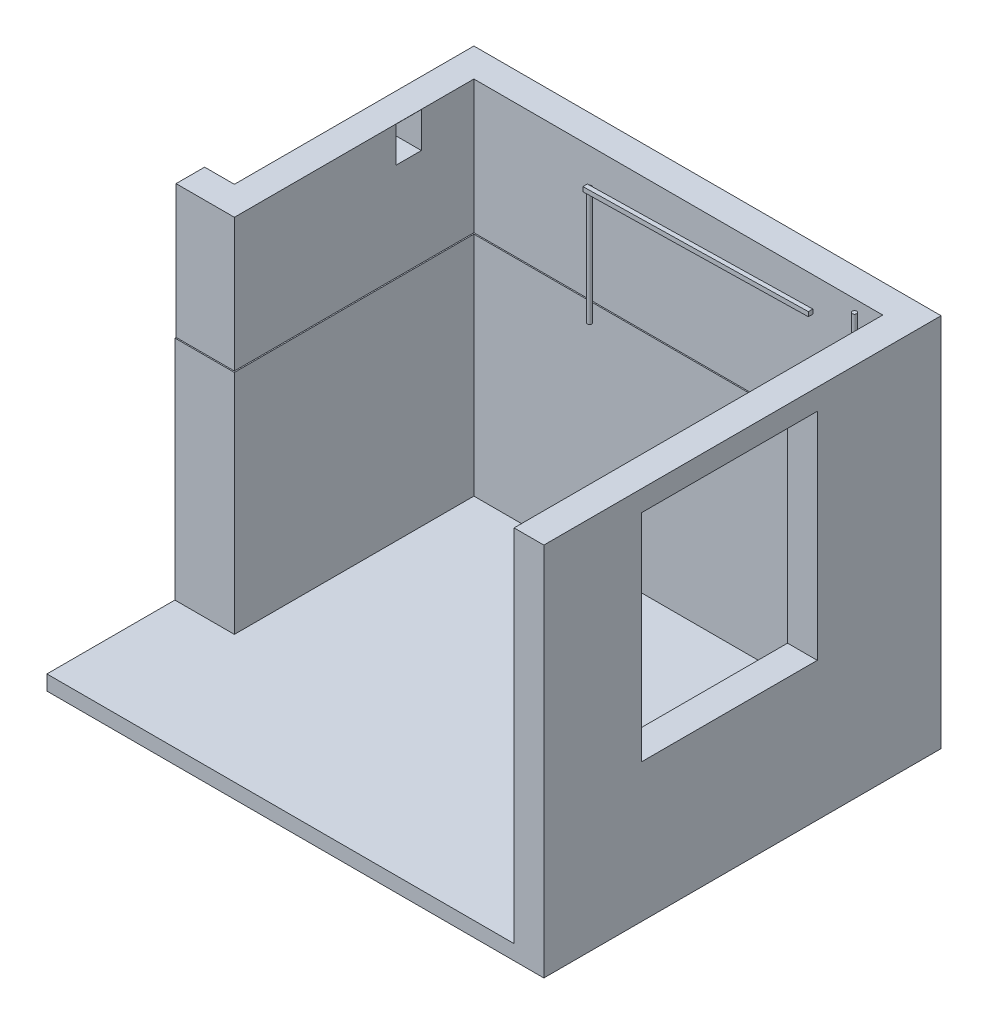
SolidWorks part; units mm, degrees
ref_plane "Спереди" through (0, 0, 0) normal (0, 0, 1) x (1, 0, 0)
ref_plane "Сверху" through (0, 0, 0) normal (0, 1, 0) x (1, 0, 0)
ref_plane "Справа" through (0, 0, 0) normal (1, 0, 0) x (0, 0, -1)
sketch "Эскиз1" plane through (0, 0, 0) normal (0, 1, 0) x (1, 0, 0)
  line L0 (0, 0) -> (0, 1610)
  line L1 (0, 1610) -> (2740, 1610)
  line L2 (2740, 1610) -> (2740, -860)
  line L3 (2740, -860) -> (-400, -860)
  line L5 (-400, 0) -> (0, 0)
  line L6 (2940, 1810) -> (-200, 1810)
  line L7 (-200, 1810) -> (-200, 200)
  line L8 (-200, 200) -> (-400, 200)
  line L9 (-400, 200) -> (-400, 0)
  line L10 (-400, -860) -> (-400, -1060)
  line L11 (-400, -1060) -> (2940, -1060)
  line L12 (2940, -1060) -> (2940, 1810)
  line L13 (2740, 1610) -> (2940, 1610) construction
  line L14 (2740, 1610) -> (2740, 1810) construction
  line L15 (0, 1610) -> (-200, 1610) construction
  line L16 (-200, 200) -> (-200, 0) construction
  line L17 (2740, -860) -> (2740, -1060) construction
  dimension "D1" = 200
  dimension "D2" = 1610
  dimension "D3" = 400
  dimension "D4" = 2470
  dimension "D5" = 2740
extrude "Бобышка-Вытянуть1" add sketch "Эскиз1" along normal blind 2420
sketch "Эскиз2" plane through (0, 0, 0) normal (0, -1, 0) x (1, 0, 0)
  line L0 (-400, 1060) -> (2940, 1060) construction
  line L1 (-400, 1060) -> (2940, 1060)
  line L2 (-200, -200) -> (-400, -200) construction
  line L3 (-200, -200) -> (-400, -200)
  line L4 (-400, -200) -> (-400, 0) construction
  line L5 (-400, -200) -> (-400, 1060)
  line L6 (-200, -1810) -> (-200, -200) construction
  line L7 (2940, -1810) -> (-200, -1810) construction
  line L8 (2940, 1060) -> (2940, -1810) construction
  line L9 (-200, -1810) -> (-200, -200)
  line L10 (2940, -1810) -> (-200, -1810)
  line L11 (2940, 1060) -> (2940, -1810)
extrude "Бобышка-Вытянуть2" add sketch "Эскиз2" along normal blind 100
sketch "Эскиз3" plane through (0, 0, 1060) normal (0, 0, 1) x (1, 0, 0)
  line L12 (-400, 2420) -> (-400, -100)
  line L13 (-400, -100) -> (2940, -100)
  line L14 (2940, -100) -> (2940, 2420)
  line L15 (2940, 2420) -> (-400, 2420)
  line L16 (-400, 2420) -> (-400, -100)
  line L17 (-400, -100) -> (2940, -100)
  line L18 (2940, -100) -> (2940, 2420)
  line L19 (2940, 2420) -> (-400, 2420)
  dimension "D1" = 0
extrude "Вырез-Вытянуть1" cut sketch "Эскиз3" against normal up to surface (200 mm away) up to face at (1170, 1210, 860)
sketch "Эскиз4" plane through (0, 0, 0) normal (1, 0, 0) x (0, 0, -1)
  line L0 (1610, 2420) -> (1610, 0) construction
  line L1 (1095, 2419) -> (1265, 2419)
  line L2 (1095, 2419) -> (1095, 2180)
  line L3 (1095, 2180) -> (1265, 2180)
  line L4 (1265, 2419) -> (1265, 2180)
  line L5 (1095, 2419) -> (1265, 2180) construction
  line L6 (1095, 2180) -> (1265, 2419) construction
  line L7 (0, 0) -> (1610, 0) construction
  point P0 (1180, 2299.5)
  dimension "D1" = 170
  dimension "D2" = 239
  dimension "D3" = 345
  dimension "D4" = 2180
extrude "Вырез-Вытянуть2" cut sketch "Эскиз4" against normal up to surface (200 mm away) up to face at (-200, 1160, -1005)
ref_plane "Плоскость1" through (0, 2235, 0) normal (0, 1, 0) x (1, 0, 0)
sketch "Эскиз5" plane through (0, 2420, 0) normal (0, 1, 0) x (1, 0, 0)
  line L0 (-400, 8) -> (-8, 8)
  line L1 (-400, 200) -> (-400, 0) construction
  line L2 (-8, 8) -> (-8, 1618)
  line L3 (-8, 1618) -> (2740, 1618)
  line L4 (2740, 1610) -> (2740, -860) construction
  line L5 (2740, 1618) -> (2740, 1610)
  line L6 (0, 0) -> (0, 1610) construction
  line L7 (0, 1610) -> (2740, 1610) construction
  line L8 (0, 0) -> (0, 1610)
  line L9 (0, 1610) -> (2740, 1610)
  line L10 (-400, 0) -> (0, 0) construction
  line L11 (-400, 0) -> (0, 0)
  line L12 (-400, 0) -> (-400, 8)
  line L13 (-8, 8) -> (-8, 0) construction
  line L14 (-8, 8) -> (0, 8) construction
  dimension "D1" = 8
extrude "Вырез-Вытянуть3" cut sketch "Эскиз5" against normal blind 895
sketch "Эскиз6" plane through (0, 2235, 0) normal (0, 1, 0) x (1, 0, 0)
  line L0 (-8, 1618) -> (-8, 8) construction
  line L1 (2740, 1618) -> (-8, 1618) construction
  circle A0 centre (824.5, 1563) radius 15
  dimension "D2" = 30
  dimension "D1" = 832.5
  dimension "D3" = 55
extrude "Бобышка-Вытянуть3" add sketch "Эскиз6" against normal blind 790 separate body
sketch "Эскиз7" plane through (0, 2420, 0) normal (0, 1, 0) x (1, 0, 0)
  line L0 (2740, 1618) -> (2740, -860) construction
  line L1 (2740, 1618) -> (-8, 1618) construction
  circle A0 centre (2630, 1538) radius 15
  dimension "D1" = 30
  dimension "D2" = 110
  dimension "D3" = 80
extrude "Бобышка-Вытянуть4" add sketch "Эскиз7" against normal up to next (2420 mm away)
ref_plane "Плоскость4" through (0, 1535, 0) normal (0, 1, 0) x (1, 0, 0)
sketch "Эскиз10" plane through (0, 1535, 0) normal (0, 1, 0) x (1, 0, 0)
  line L0 (2740, 1618) -> (-8, 1618) construction
  line L1 (2470, 1598) -> (2280, 1598)
  line L2 (2470, 1598) -> (2470, 1458)
  line L3 (2470, 1458) -> (2280, 1458)
  line L4 (2280, 1598) -> (2280, 1458)
  line L5 (2470, 1598) -> (2280, 1458) construction
  line L6 (2470, 1458) -> (2280, 1598) construction
  line L7 (2740, 1618) -> (2740, -860) construction
  point P0 (2375, 1528)
  dimension "D1" = 190
  dimension "D2" = 140
  dimension "D3" = 20
  dimension "D4" = 365
extrude "Бобышка-Вытянуть6" add sketch "Эскиз10" along normal blind 230 separate body
ref_plane "Плоскость5" through (0, 0, -1563) normal (0, 0, 1) x (1, 0, 0)
sketch "Эскиз12" plane through (0, 0, -1563) normal (0, 0, 1) x (1, 0, 0)
  line L0 (0, 1525) -> (2740, 1525) construction
  line L1 (809.5, 2215) -> (2325, 2245)
  line L2 (809.5, 2215) -> (809.5, 2245)
  line L3 (809.5, 2245) -> (2325, 2275)
  line L4 (2325, 2245) -> (2325, 2275)
  line L5 (2740, 1525) -> (2740, 2420) construction
  line L7 (809.5, 2235) -> (809.5, 1445) construction
  dimension "D1" = 690
  dimension "D2" = 720
  dimension "D3" = 30
  dimension "D4" = 415
extrude "Бобышка-Вытянуть7" add sketch "Эскиз12" along normal blind 30
sketch "Эскиз13" plane through (2940, 0, 0) normal (1, 0, 0) x (0, 0, -1)
  line L1 (978, 2280) -> (-202, 2280)
  line L2 (978, 2280) -> (978, 830)
  line L3 (978, 830) -> (-202, 830)
  line L4 (-202, 2280) -> (-202, 830)
  line L5 (978, 2280) -> (-202, 830) construction
  line L6 (978, 830) -> (-202, 2280) construction
  line L7 (1618, 1525) -> (1618, 2420) construction
  line L8 (1610, 0) -> (-860, 0) construction
  point P0 (388, 1555)
  dimension "D1" = 1180
  dimension "D2" = 1450
  dimension "D3" = 830
  dimension "D4" = 640
extrude "Вырез-Вытянуть4" cut sketch "Эскиз13" against normal blind 400
